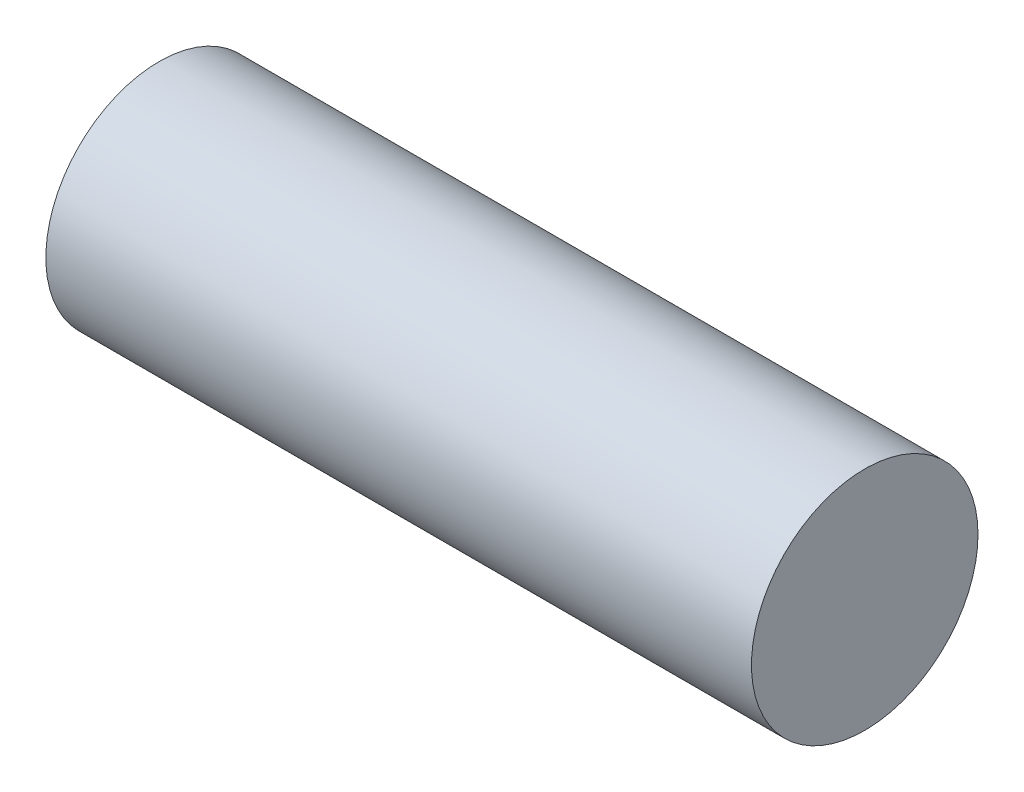
SolidWorks part; units mm, degrees
ref_plane "Face" through (0, 0, 0) normal (0, 0, 1) x (1, 0, 0)
ref_plane "Dessus" through (0, 0, 0) normal (0, 1, 0) x (1, 0, 0)
ref_plane "Droite" through (0, 0, 0) normal (1, 0, 0) x (0, 0, -1)
sketch "Esquisse1" plane through (0, 0, 0) normal (1, 0, 0) x (0, 0, -1)
  circle A0 centre (0, 0) radius 16.1
  dimension "D1" = 32.2
extrude "Boss.-Extru.1" add sketch "Esquisse1" along normal blind 100.3
sketch "Esquisse2" plane through (0, 0, 0) normal (-1, 0, 0) x (0, 0, 1)
  line L0 (-9, 2.7207) -> (1, 2.7207)
  line L1 (1, 2.7207) -> (1, -2.2793)
  line L2 (1, -2.2793) -> (-9, -2.2793)
  line L3 (-9, -2.2793) -> (-9, 2.7207)
  circle A0 centre (0, 0) radius 16.1 construction
  dimension "D1" = 10
  dimension "D2" = 5
  dimension "D3" = 1
extrude "Enlèv. mat.-Extru.1" cut sketch "Esquisse2" against normal blind 10
sketch "Esquisse3" plane through (0, 0, 0) normal (-1, 0, 0) x (0, 0, 1)
  line L0 (3.9905, -1.5) -> (11.9905, -1.5)
  line L1 (5.9905, 0) -> (9.9905, 0)
  arc A0 (3.9905, -1.5) -> (5.9905, 0) centre (5.7405, -1.75) cw
  arc A1 (9.9905, 0) -> (11.9905, -1.5) centre (10.2405, -1.75) cw
  dimension "D2" = 8
extrude "Enlèv. mat.-Extru.2" cut sketch "Esquisse3" against normal blind 10
